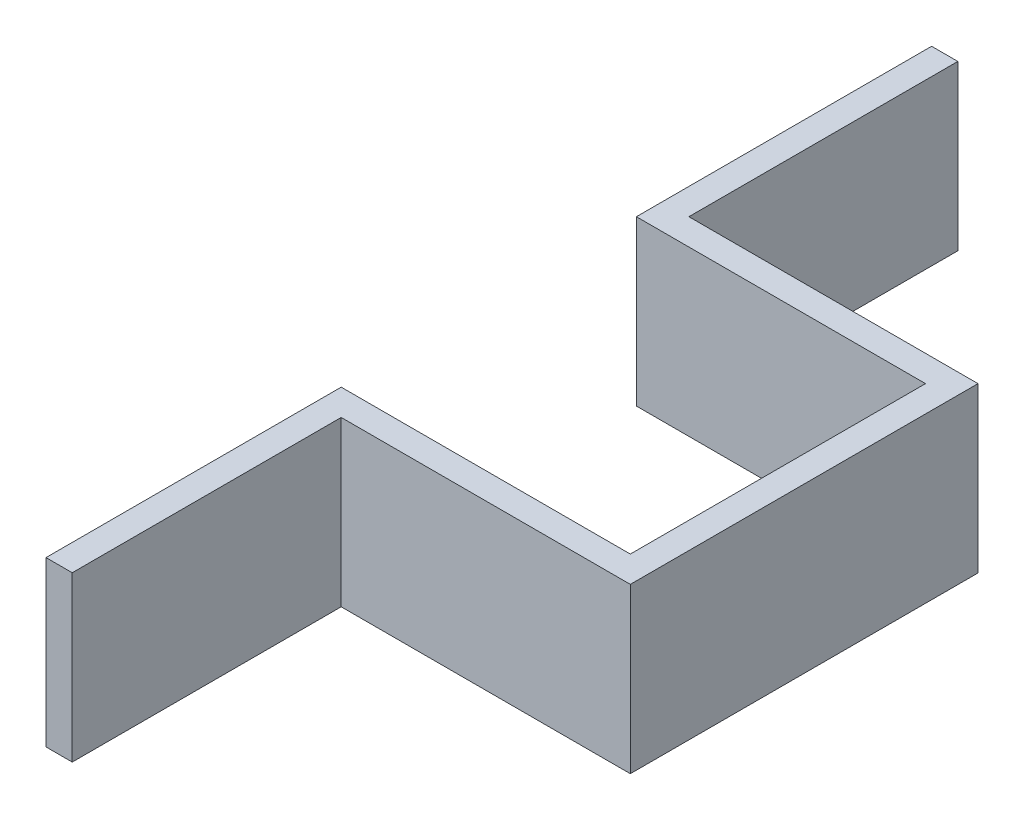
SolidWorks part; units mm, degrees
ref_plane "Front Plane" through (0, 0, 0) normal (0, 0, 1) x (1, 0, 0)
ref_plane "Top Plane" through (0, 0, 0) normal (0, 1, 0) x (1, 0, 0)
ref_plane "Right Plane" through (0, 0, 0) normal (1, 0, 0) x (0, 0, -1)
ref_plane "Plane1" through (0, 5, 0) normal (0, 1, 0) x (1, 0, 0)
sketch "Sketch1" plane through (0, 5, 0) normal (0, 1, 0) x (1, 0, 0)
  line B0 (194.1023, 302.5) -> (190.1023, 302.5)
  line B1 (190.1023, 302.5) -> (190.1023, 257.5)
  line B2 (190.1023, 257.5) -> (234.1745, 257.5)
  line B3 (234.1745, 257.5) -> (234.1745, 212.5)
  line B4 (234.1745, 212.5) -> (190.1023, 212.5)
  line B5 (190.1023, 212.5) -> (190.1023, 167.5)
  line B6 (190.1023, 167.5) -> (194.1023, 167.5)
  line B7 (194.1023, 167.5) -> (194.1023, 208.5)
  line B8 (194.1023, 208.5) -> (238.1745, 208.5)
  line B9 (238.1745, 208.5) -> (238.1745, 261.5)
  line B10 (238.1745, 261.5) -> (194.1023, 261.5)
  line B11 (194.1023, 261.5) -> (194.1023, 302.5)
sketch_block_instance "Block1-1"
sketch_block "Block1"
extrude "Boss-Extrude1" add sketch "Sketch1" against normal blind 25
